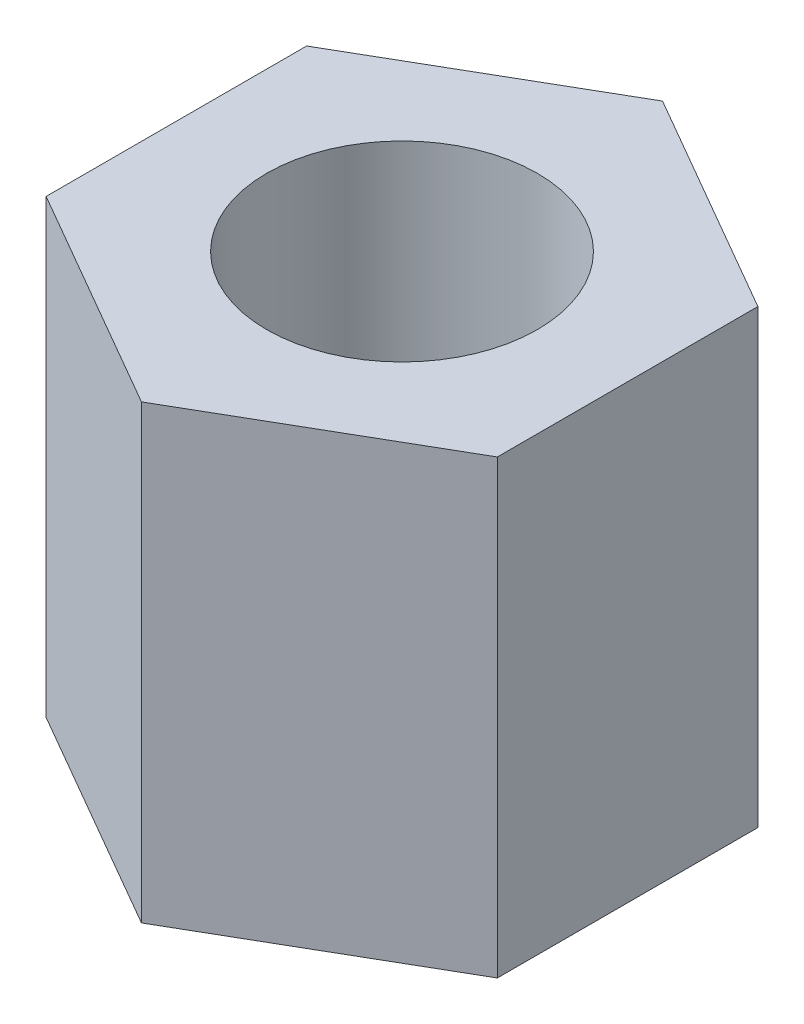
SolidWorks part; units mm, degrees
ref_plane "Piano frontale" through (0, 0, 0) normal (0, 0, 1) x (1, 0, 0)
ref_plane "Piano superiore" through (0, 0, 0) normal (0, 1, 0) x (1, 0, 0)
ref_plane "Piano destro" through (0, 0, 0) normal (1, 0, 0) x (0, 0, -1)
sketch "Sketch1" plane through (0, 0, 0) normal (0, 1, 0) x (1, 0, 0)
  line L1 (-34.9518, 17.0938) -> (-37.4518, 15.6504)
  line L2 (-37.4518, 15.6504) -> (-37.4518, 12.7637)
  line L3 (-37.4518, 12.7637) -> (-34.9518, 11.3203)
  line L4 (-34.9518, 11.3203) -> (-32.4518, 12.7637)
  line L5 (-32.4518, 12.7637) -> (-32.4518, 15.6504)
  line L6 (-32.4518, 15.6504) -> (-34.9518, 17.0938)
  circle A0 centre (-34.9518, 14.207) radius 2.5 construction
  circle A1 centre (-34.9518, 14.207) radius 1.5
  dimension "D1" = 3
  dimension "D2" = 5
extrude "Boss-Extrude1" add sketch "Sketch1" along normal blind 5
